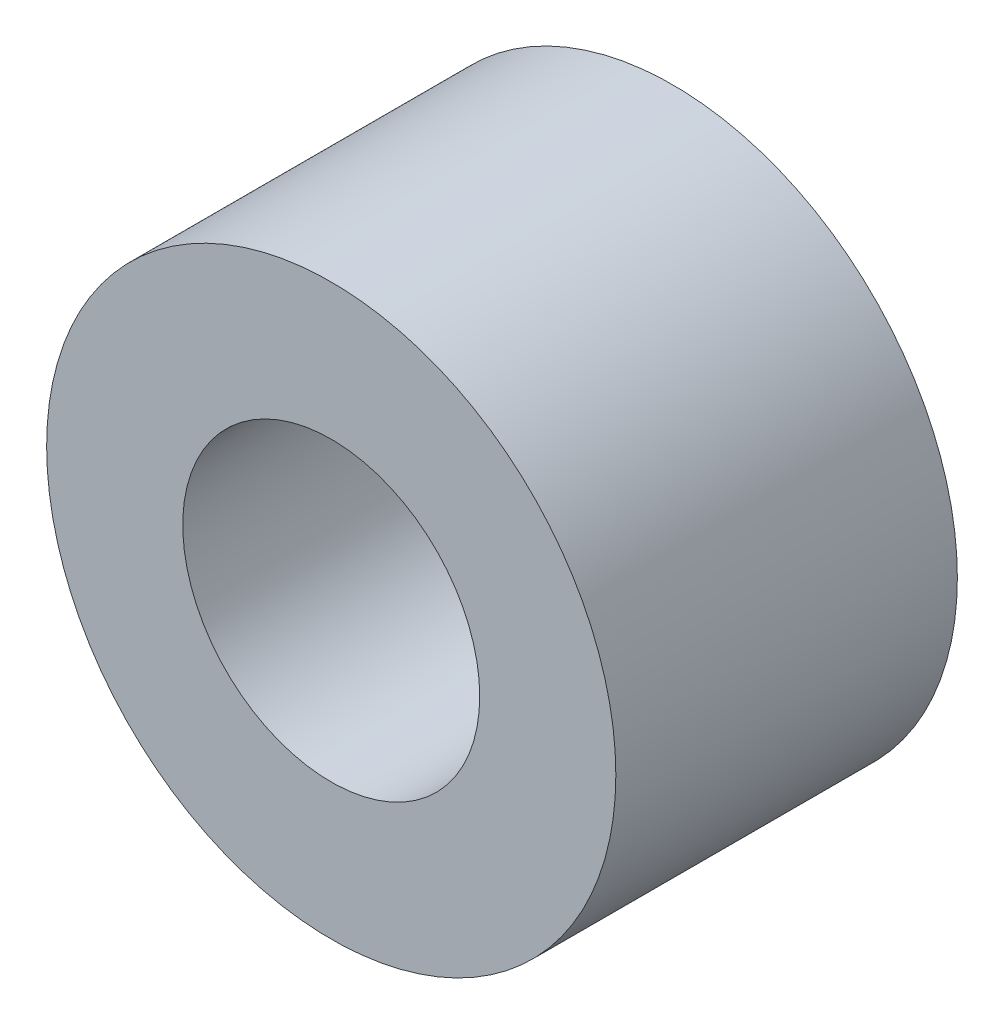
SolidWorks part; units mm, degrees
ref_plane "Plan de face" through (0, 0, 0) normal (0, 0, 1) x (1, 0, 0)
ref_plane "Plan de dessus" through (0, 0, 0) normal (0, 1, 0) x (1, 0, 0)
ref_plane "Plan de droite" through (0, 0, 0) normal (1, 0, 0) x (0, 0, -1)
sketch "Esquisse1" plane through (0, 0, 0) normal (0, 0, 1) x (1, 0, 0)
  circle A0 centre (0, 0) radius 11.5
  circle A1 centre (0, 0) radius 6
  dimension "D1" = 12
  dimension "D2" = 23
extrude "Boss.-Extru.1" add sketch "Esquisse1" along normal blind 13.8
